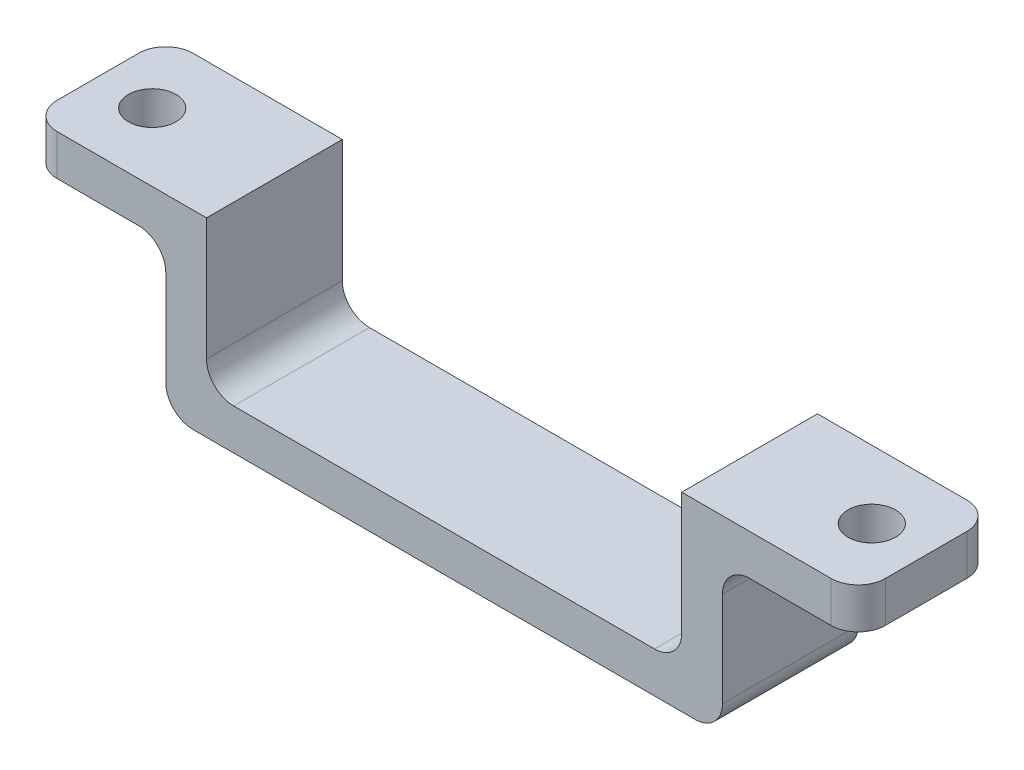
SolidWorks part; units mm, degrees
ref_plane "Front Plane" through (0, 0, 0) normal (0, 0, 1) x (1, 0, 0)
ref_plane "Top Plane" through (0, 0, 0) normal (0, 1, 0) x (1, 0, 0)
ref_plane "Right Plane" through (0, 0, 0) normal (1, 0, 0) x (0, 0, -1)
sketch "Sketch1" plane through (0, 0, 0) normal (0, 0, 1) x (1, 0, 0)
  line L0 (-30.5, 0) -> (-17.5, 0)
  line L1 (-17.5, 0) -> (-17.5, -11)
  line L2 (-17.5, -11) -> (17.5, -11)
  line L3 (17.5, -11) -> (17.5, 0)
  line L4 (17.5, 0) -> (30.5, 0)
  point P3 (0, -11)
  dimension "D1" = 35
  dimension "D2" = 13
  dimension "D3" = 11
extrude "Extrude-Thin1" add sketch "Sketch1" along normal mid plane 10 thin
fillet "Fillet1" radius 2 6 edges at (17.5, -11, 0) (-17.5, -11, 0) (-20.5, -3, 0) (20.5, -3, 0) (20.5, -14, 0) (-20.5, -14, 0)
fillet "Fillet2" radius 2 4 edges at (30.5, -1.5, 5) (30.5, -1.5, -5) (-30.5, -1.5, -5) (-30.5, -1.5, 5)
sketch "Sketch2" plane through (0, -3, 0) normal (0, -1, 0) x (-1, 0, 0)
  line L0 (-26.5, 0) -> (26.5, 0) construction
  line L1 (-30.5, -3) -> (-30.5, 3) construction
  circle A0 centre (-26.5, 0) radius 1.75
  circle A1 centre (26.5, 0) radius 1.75
  point P4 (0, 0)
  point P6 (-30.5, 0)
  dimension "D1" = 3.5
  dimension "D2" = 4
extrude "Cut-Extrude1" cut sketch "Sketch2" against normal through all
